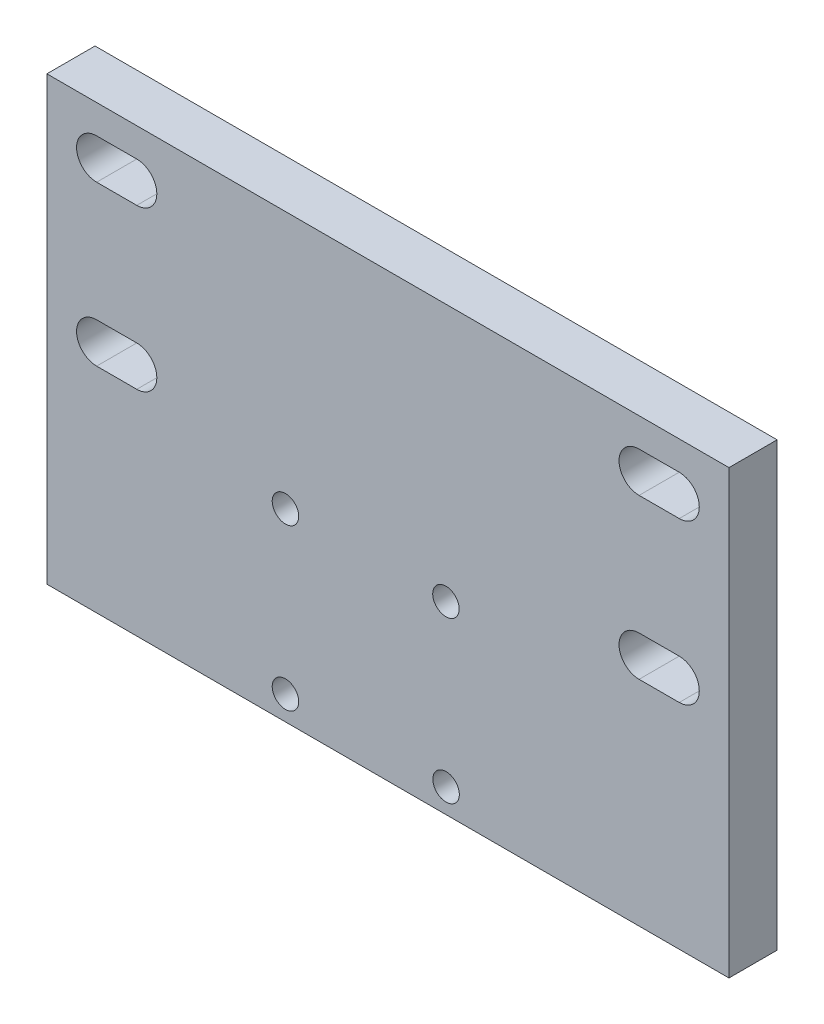
SolidWorks part; units mm, degrees
ref_plane "Front Plane" through (0, 0, 0) normal (0, 0, 1) x (1, 0, 0)
ref_plane "Top Plane" through (0, 0, 0) normal (0, 1, 0) x (1, 0, 0)
ref_plane "Right Plane" through (0, 0, 0) normal (1, 0, 0) x (0, 0, -1)
sketch "Sketch2" plane through (0, 0, 0) normal (0, 0, 1) x (1, 0, 0)
  line L0 (-40, -39.1363) -> (45, -39.1363)
  line L1 (-33.8, 9.85) -> (-28.8, 9.85) construction
  line L2 (-33.8, 12.35) -> (-28.8, 12.35)
  line L3 (-33.8, 7.35) -> (-28.8, 7.35)
  line L4 (45, 15.9473) -> (45, -39.1363)
  line L5 (-12.1553, 15.9473) -> (29.8303, -39.1363) construction
  line L6 (-29.8303, -39.1363) -> (12.1553, 15.9473) construction
  line L7 (-40, 15.9473) -> (45, 15.9473)
  line L8 (-40, 15.9473) -> (-40, -39.1363)
  line L9 (-33.8, -10) -> (-28.8, -10) construction
  line L10 (-33.8, -7.5) -> (-28.8, -7.5)
  line L11 (-33.8, -12.5) -> (-28.8, -12.5)
  line L12 (2.5, 15.9473) -> (2.5, -39.1363) construction
  line L13 (38.8, 9.85) -> (33.8, 9.85) construction
  line L14 (38.8, 12.35) -> (33.8, 12.35)
  line L15 (38.8, 7.35) -> (33.8, 7.35)
  line L16 (38.8, -10) -> (33.8, -10) construction
  line L17 (38.8, -7.5) -> (33.8, -7.5)
  line L18 (38.8, -12.5) -> (33.8, -12.5)
  arc A0 (38.8, 12.35) -> (38.8, 7.35) centre (38.8, 9.85) cw
  arc A1 (33.8, 7.35) -> (33.8, 12.35) centre (33.8, 9.85) cw
  arc A2 (38.8, -7.5) -> (38.8, -12.5) centre (38.8, -10) cw
  arc A3 (33.8, -12.5) -> (33.8, -7.5) centre (33.8, -10) cw
  circle A4 centre (-10.2688, -16.1316) radius 1.65
  circle A5 centre (9.7312, -16.1316) radius 1.65
  circle A6 centre (-10.2688, -36.1316) radius 1.65
  circle A7 centre (9.7477, -36.1316) radius 1.65
  arc A8 (-33.8, 12.35) -> (-33.8, 7.35) centre (-33.8, 9.85) ccw
  arc A9 (-28.8, 7.35) -> (-28.8, 12.35) centre (-28.8, 9.85) ccw
  arc A10 (-33.8, -7.5) -> (-33.8, -12.5) centre (-33.8, -10) ccw
  arc A11 (-28.8, -12.5) -> (-28.8, -7.5) centre (-28.8, -10) ccw
  point P2 (36.3, 9.85)
  point P8 (0, 0)
  point P29 (-31.3, 9.85)
  point P35 (-31.3, -10)
  point P44 (36.3, -10)
  dimension "D3" = 67.6
  dimension "D4" = 67.6
  dimension "D12" = 3.3
  dimension "D13" = 3.3
  dimension "D14" = 3.3
  dimension "D15" = 3.3
  dimension "D10" = 20
  dimension "D11" = 20
  dimension "D16" = 20
  dimension "D17" = 85
  dimension "D20" = 5
  dimension "D21" = 5
  dimension "D22" = 5
  dimension "D23" = 5
extrude "Boss-Extrude1" add sketch "Sketch2" along normal blind 6
